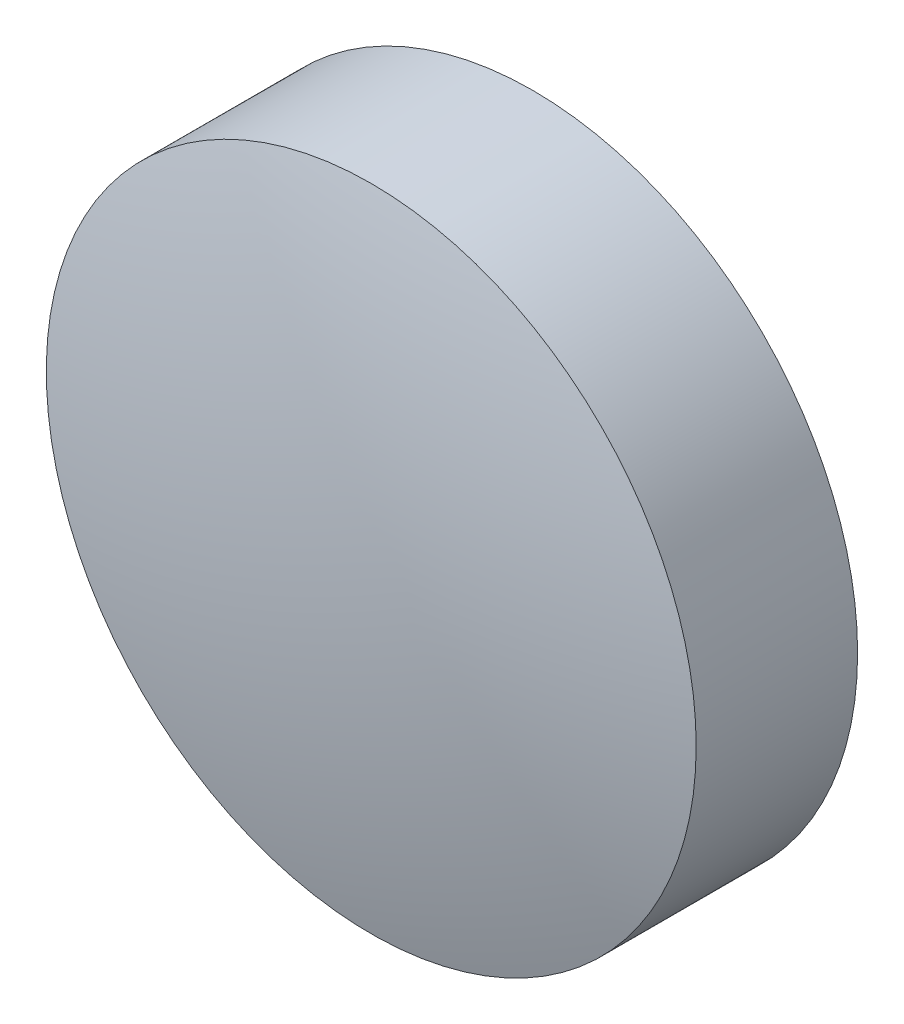
SolidWorks part; units mm, degrees
material "Sklo"
ref_plane "Přední rovina" through (0, 0, 0) normal (0, 0, 1) x (1, 0, 0)
ref_plane "Horní rovina" through (0, 0, 0) normal (0, 1, 0) x (1, 0, 0)
ref_plane "Pravá rovina" through (0, 0, 0) normal (1, 0, 0) x (0, 0, -1)
sketch "Skica1" plane through (0, 0, 0) normal (1, 0, 0) x (0, 0, -1)
  line L0 (-1.3318, 6.25) -> (1.773, 6.25)
  line L1 (-65.3539, 0) -> (70.2006, 0) construction
  line L2 (-2.15, 0) -> (2.15, 0)
  arc A0 (-1.3318, 6.25) -> (-2.15, 0) centre (22.13, 0) ccw
  arc A1 (1.773, 6.25) -> (2.15, 0) centre (-49.85, 0) cw
  dimension "D2" = 24.28
  dimension "D3" = 52
  dimension "D1" = 12.5
  dimension "D4" = 4.3
  dimension "D5" = 3.1048
  dimension "D6" = 3.1048
revolve "Rotovat1" add sketch "Skica1" angle 360 about L1
